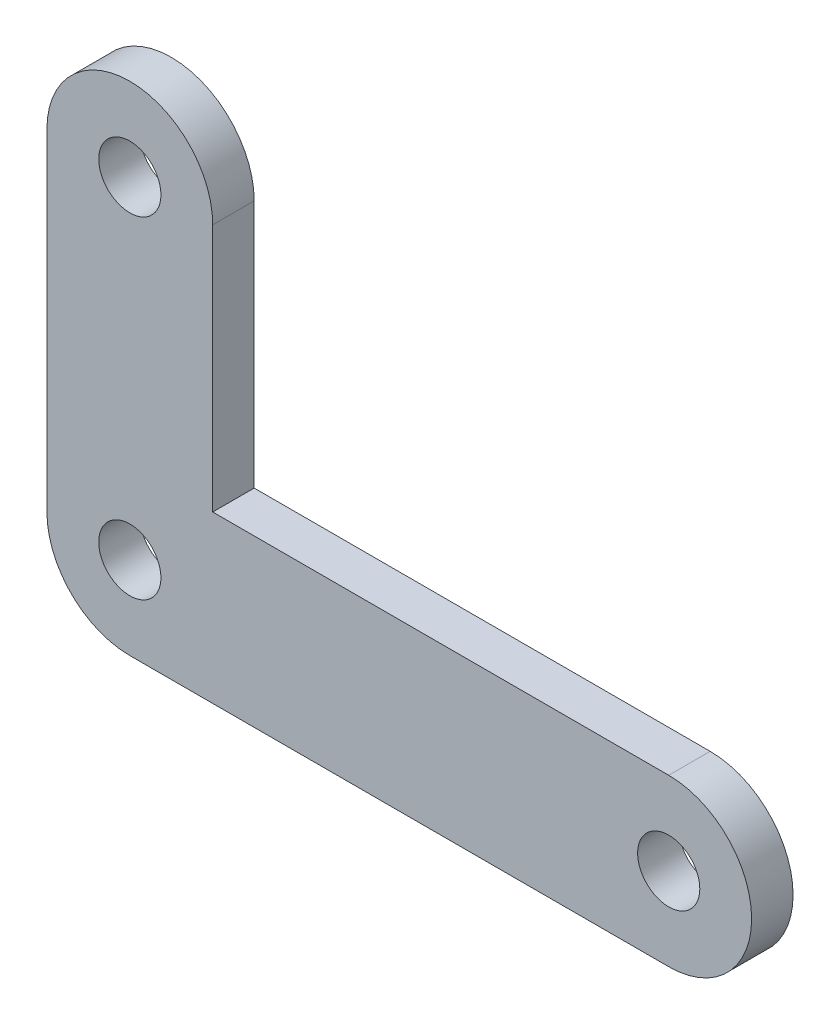
SolidWorks part; units mm, degrees
ref_plane "Front Plane" through (0, 0, 0) normal (0, 0, 1) x (1, 0, 0)
ref_plane "Top Plane" through (0, 0, 0) normal (0, 1, 0) x (1, 0, 0)
ref_plane "Right Plane" through (0, 0, 0) normal (1, 0, 0) x (0, 0, -1)
sketch "Sketch1" plane through (0, 0, 0) normal (0, 0, 1) x (1, 0, 0)
  line L0 (0, 0) -> (-82.55, 0) construction
  line L1 (0, -12.7) -> (-82.55, -12.7)
  line L2 (0, 12.7) -> (-82.55, 12.7)
  line L3 (-82.55, 0) -> (-82.55, 50.8) construction
  line L4 (-95.25, 0) -> (-95.25, 50.8)
  line L5 (-69.85, 0) -> (-69.85, 50.8)
  arc A0 (0, -12.7) -> (0, 12.7) centre (0, 0) ccw
  arc A1 (-82.55, 12.7) -> (-82.55, -12.7) centre (-82.55, 0) ccw
  arc A2 (-95.25, 0) -> (-69.85, 0) centre (-82.55, 0) ccw
  arc A3 (-69.85, 50.8) -> (-95.25, 50.8) centre (-82.55, 50.8) ccw
  circle A4 centre (0, 0) radius 4.7625
  circle A5 centre (-82.55, 0) radius 4.7625
  circle A6 centre (-82.55, 50.8) radius 4.7625
  point P3 (-41.275, 0)
  point P8 (-82.55, 25.4)
  dimension "D4" = 9.525
  dimension "D1" = 82.55
  dimension "D2" = 50.8
  dimension "D3" = 25.4
extrude "Boss-Extrude1" add sketch "Sketch1" along normal blind 6.35 contours L5 A3 L4 A1 L2 A6 | A1 A2 L5 L2 A5 | A2 L1 A0 L2 L5 A4
